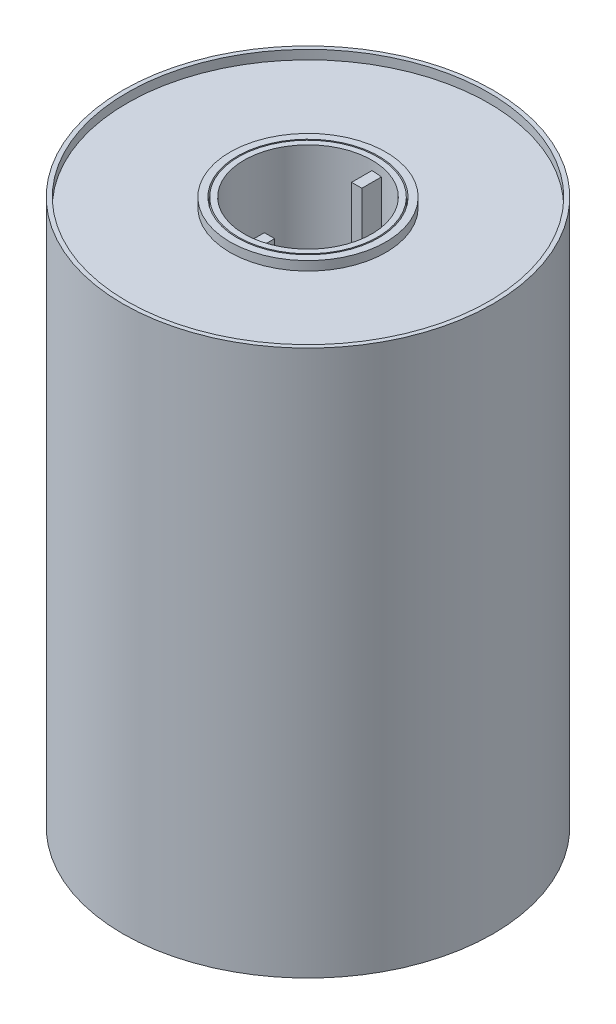
SolidWorks part; units mm, degrees
ref_plane "Alzado" through (0, 0, 0) normal (0, 0, 1) x (1, 0, 0)
ref_plane "Planta" through (0, 0, 0) normal (0, 1, 0) x (1, 0, 0)
ref_plane "Vista lateral" through (0, 0, 0) normal (1, 0, 0) x (0, 0, -1)
sketch "Croquis1" plane through (0, 0, 0) normal (0, 1, 0) x (1, 0, 0)
  circle A0 centre (0, 0) radius 50.8901
extrude "Saliente-Extruir1" add sketch "Croquis1" along normal blind 150
sketch "Croquis2" plane through (0, 150, 0) normal (0, 1, 0) x (1, 0, 0)
  circle A0 centre (0, 0) radius 17.5714
extrude "Cortar-Extruir1" cut sketch "Croquis2" against normal through all
sketch "Croquis3" plane through (0, 150, 0) normal (0, 1, 0) x (1, 0, 0)
  circle A0 centre (0, 0) radius 19.1218
  circle A1 centre (0, 0) radius 49.7184
extrude "Cortar-Extruir2" cut sketch "Croquis3" against normal blind 2.5
sketch "Croquis4" plane through (0, 0, 0) normal (0, -1, 0) x (1, 0, 0)
  circle A0 centre (0, 0) radius 17.8298
  circle A1 centre (0, 0) radius 19.4769
extrude "Saliente-Extruir3" add sketch "Croquis4" along normal blind 15
sketch "Croquis6" plane through (0, 0, 0) normal (0, -1, 0) x (1, 0, 0)
  circle A0 centre (0, 0) radius 21.5317
  circle A1 centre (0, 0) radius 49.2332
extrude "Cortar-Extruir4" cut sketch "Croquis6" against normal blind 5
sketch "Croquis8" plane through (0, 147.5, 0) normal (0, 1, 0) x (1, 0, 0)
  line L1 (0, 17.5714) -> (2.814, 17.5714)
  line L2 (0, 17.5714) -> (0, 11.9953)
  line L3 (0, 11.9953) -> (2.814, 11.9953)
  line L4 (2.814, 17.5714) -> (2.814, 11.9953)
  line L5 (0, -17.5714) -> (2.814, -17.5714)
  line L6 (0, -17.5714) -> (0, -11.9953)
  line L7 (0, -11.9953) -> (2.814, -11.9953)
  line L8 (2.814, -17.5714) -> (2.814, -11.9953)
  circle A0 centre (0, 0) radius 17.5714 construction
  point P10 (0, 0)
  point P11 (0, 0)
  point P12 (0, 0)
extrude "Saliente-Extruir6" add sketch "Croquis8" against normal blind 145
sketch "Croquis9" plane through (0, 147.5, 0) normal (0, 1, 0) x (1, 0, 0)
  circle A0 centre (0, 0) radius 19.463
  circle A1 centre (0, 0) radius 21.4211
extrude "Saliente-Extruir7" add sketch "Croquis9" along normal blind 2.5
